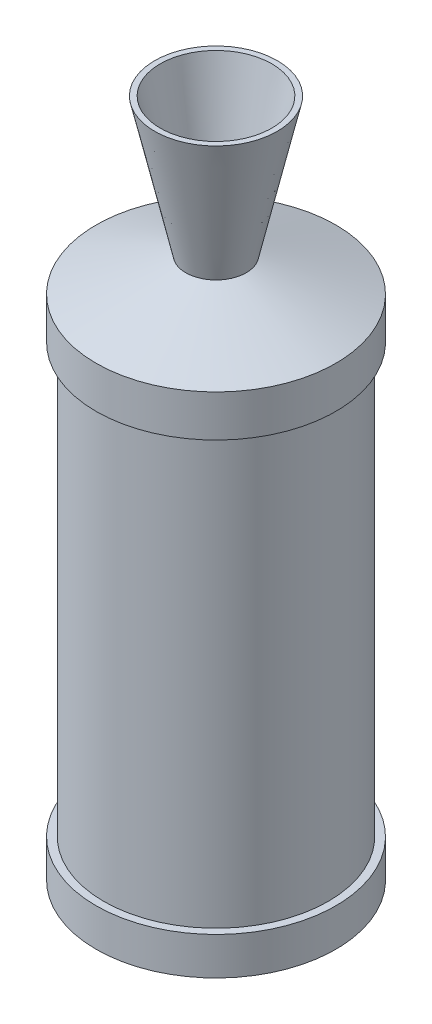
SolidWorks part; units mm, degrees
material "Commercially Pure CP-Ti UNS R50400 (SS)"
ref_plane "Front Plane" through (0, 0, 0) normal (0, 0, 1) x (1, 0, 0)
ref_plane "Top Plane" through (0, 0, 0) normal (0, 1, 0) x (1, 0, 0)
ref_plane "Right Plane" through (0, 0, 0) normal (1, 0, 0) x (0, 0, -1)
sketch "Sketch1" plane through (0, 0, 0) normal (0, 0, 1) x (1, 0, 0)
  line L0 (0, 0) -> (279.4, 0) construction
  line L1 (102.37, 0) -> (102.37, 514.35) construction
  line L2 (102.37, 34.44) -> (434.7994, 34.44) construction
  line L3 (109.297, 34.44) -> (109.297, 895.35) construction
  line L4 (109.297, 68.84) -> (-39.6106, 68.84) construction
  line L5 (102.37, 459.22) -> (711.3913, 459.22) construction
  line L6 (109.297, 497.22) -> (-188.2082, 497.22) construction
  line L7 (0, 0) -> (0, 876.3) construction
  line L8 (0, 527.83) -> (410.1256, 527.83) construction
  line L9 (0, 653.67) -> (316.3906, 653.67) construction
  line L10 (0, 0) -> (19, 0)
  line L11 (19, 0) -> (102.37, 34.44)
  line L12 (102.37, 34.44) -> (109.297, 34.44)
  line L13 (109.297, 34.44) -> (109.297, 68.84)
  line L14 (109.297, 68.84) -> (102.37, 68.84)
  line L15 (102.37, 68.84) -> (102.37, 459.22)
  line L16 (102.37, 459.22) -> (109.297, 459.22)
  line L17 (109.297, 459.22) -> (109.297, 497.22)
  line L18 (109.297, 497.22) -> (27.555, 527.83)
  line L19 (27.555, 527.83) -> (55.87, 653.67)
  line L20 (0, 4) -> (82.2452, 4) construction
  line L21 (19, 0) -> (19, 38.1) construction
  line L22 (102.37, 34.44) -> (72.8556, 34.44) construction
  line L23 (98.37, 34.44) -> (98.37, 813.7021) construction
  line L24 (0, 0) -> (0, 4)
  line L25 (0, 4) -> (19, 4)
  line L26 (19, 4) -> (98.37, 34.44)
  line L27 (98.37, 34.44) -> (98.37, 497.22)
  line L28 (31.1633, 527.83) -> (-71.6827, 650.3971) construction
  line L29 (31.1633, 527.83) -> (69.85, 425.45) construction
  line L30 (-7.404, 573.7927) -> (35.714, 564.0908) construction
  line L31 (52.372, 471.7035) -> (68.426, 512.525) construction
  line L32 (31.6204, 565.0119) -> (50.87, 653.67)
  line L33 (50.87, 653.67) -> (55.87, 653.67)
  line L34 (67.0115, 508.9283) -> (98.37, 497.22)
  line L35 (6.35, 12.7) -> (95.357, 42.6531)
  line L36 (95.357, 491.6004) -> (6.35, 508)
  line L37 (95.357, 42.6531) -> (95.357, 491.6004)
  line L38 (6.35, 508) -> (6.35, 12.7)
  circle A0 centre (31.1633, 527.83) radius 20 construction
  circle A1 centre (-7.404, 573.7927) radius 40 construction
  circle A2 centre (52.372, 471.7035) radius 40 construction
  arc A3 (38.2329, 509.1212) -> (18.3075, 543.1509) centre (31.1633, 527.83) cw
  arc A4 (18.3075, 543.1509) -> (31.6204, 565.0119) centre (-7.404, 573.7927) ccw
  arc A5 (38.2329, 509.1212) -> (67.0115, 508.9283) centre (52.372, 471.7035) cw
  point P0 (0, 0)
  point P4 (102.37, 0)
  point P7 (102.37, 34.44)
  point P8 (19, 0)
  point P11 (109.297, 34.44)
  point P14 (109.297, 68.84)
  point P17 (102.37, 68.84)
  point P18 (102.37, 459.22)
  point P21 (109.297, 459.22)
  point P22 (109.297, 497.22)
  point P25 (0, 497.22)
  point P27 (0, 527.83)
  point P30 (27.555, 527.83)
  point P31 (11.1633, 527.83)
  point P32 (0, 653.67)
  point P35 (55.87, 653.67)
  point P36 (0, 4)
  point P44 (19, 4)
  point P46 (98.37, 34.44)
  point P50 (31.1633, 527.83)
  point P55 (52.372, 471.7035)
  point P58 (-7.404, 573.7927)
  point P69 (50.87, 653.67)
  point P70 (6.35, 12.7)
  point P73 (6.35, 508)
  dimension "D1" = 102.37
  dimension "D2" = 34.44
  dimension "D3" = 19
  dimension "D4" = 6.927
  dimension "D5" = 34.4
  dimension "D6" = 390.38
  dimension "D7" = 38
  dimension "D8" = 30.61
  dimension "D9" = 27.555
  dimension "D10" = 11.1633
  dimension "D11" = 125.84
  dimension "D12" = 55.87
  dimension "D13" = 4
  dimension "WHALL_C" = 4
  dimension "D14" = 60
  dimension "R_INTERNAL" = 20
  dimension "D15" = 60
  dimension "D16" = 5
revolve "Revolve1" add sketch "Sketch1" angle 360 about L7
equation "\"D13@Sketch1\" = \"WHALL_C\""
equation "\"D14@Sketch1\" = \"R_INTERNAL\"*3"
equation "\"D15@Sketch1\" = \"R_INTERNAL\"*3"
